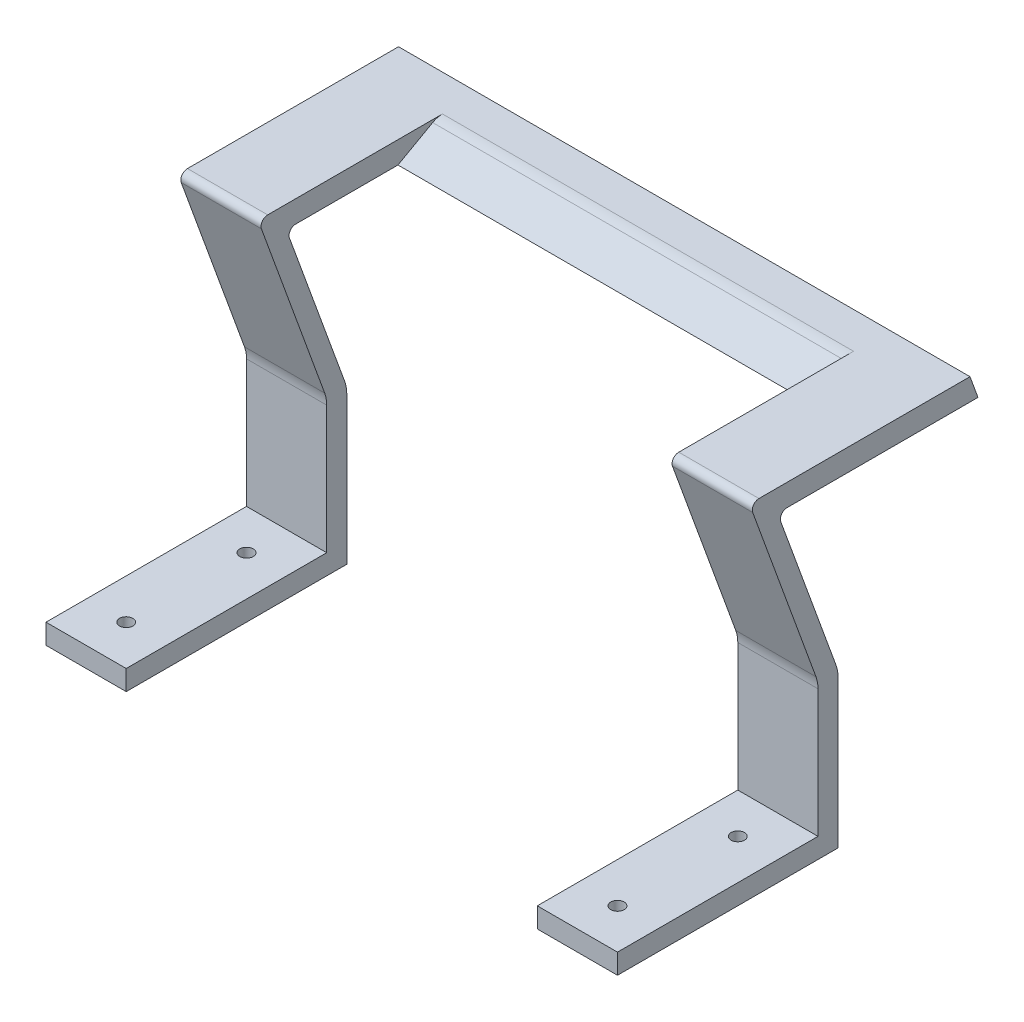
SolidWorks part; units mm, degrees
ref_plane "Front Plane" through (0, 0, 0) normal (0, 0, 1) x (1, 0, 0)
ref_plane "Top Plane" through (0, 0, 0) normal (0, 1, 0) x (1, 0, 0)
ref_plane "Right Plane" through (0, 0, 0) normal (1, 0, 0) x (0, 0, -1)
sketch "Sketch1" plane through (0, 0, 0) normal (0, 1, 0) x (1, 0, 0)
  line L0 (0, 0) -> (0, 33)
  line L1 (0, 33) -> (12, 33)
  line L2 (12, 33) -> (12, 0)
  line L3 (12, 0) -> (0, 0)
  line L4 (73.5, 33) -> (73.5, 0)
  line L5 (73.5, 0) -> (85.5, 0)
  line L6 (85.5, 0) -> (85.5, 33)
  line L7 (85.5, 33) -> (73.5, 33)
  circle A0 centre (6, 24) radius 1
  circle A1 centre (6, 6) radius 1
  circle A2 centre (79.5, 24) radius 1
  circle A3 centre (79.5, 6) radius 1
  point P17 (0, 0)
  point P18 (0, 0)
  point P19 (0, 0)
  point P20 (0, 0)
  point P21 (0, 0)
  dimension "D10" = 6
  dimension "D11" = 2
  dimension "D12" = 2
  dimension "D13" = 2
  dimension "D14" = 2
  dimension "D1" = 33
  dimension "D2" = 12
  dimension "D3" = 12
  dimension "D4" = 61.5
  dimension "D5" = 9
  dimension "D6" = 18
  dimension "D7" = 9
  dimension "D8" = 18
  dimension "D9" = 6
extrude "Boss-Extrude1" add sketch "Sketch1" along normal blind 3
sketch "Sketch2" plane through (0, 3, 0) normal (0, 1, 0) x (1, 0, 0)
  line L0 (0, 33) -> (0, 30)
  line L1 (0, 33) -> (0, 0) construction
  line L2 (0, 30) -> (12, 30)
  line L3 (12, 0) -> (12, 33) construction
  line L4 (12, 30) -> (12, 33)
  line L5 (12, 33) -> (0, 33)
  line L6 (73.5, 33) -> (85.5, 33)
  line L7 (85.5, 33) -> (85.5, 30)
  line L8 (85.5, 0) -> (85.5, 33) construction
  line L9 (85.5, 30) -> (73.5, 30)
  line L10 (73.5, 33) -> (73.5, 0) construction
  line L11 (73.5, 30) -> (73.5, 33)
  dimension "D1" = 3
extrude "Boss-Extrude2" add sketch "Sketch2" along normal blind 20
sketch "Sketch3" plane through (0, 23, 0) normal (0, 1, 0) x (1, 0, 0)
  line L0 (73.5, 33) -> (73.5, 30)
  line L1 (73.5, 30) -> (85.5, 30)
  line L2 (85.5, 30) -> (85.5, 33)
  line L3 (85.5, 33) -> (73.5, 33)
  line L4 (0, 33) -> (12, 33)
  line L5 (12, 33) -> (12, 30)
  line L6 (12, 30) -> (0, 30)
  line L7 (0, 30) -> (0, 33)
sketch "Sketch4" plane through (0, 0, 0) normal (1, 0, 0) x (0, 0, -1)
  line L0 (30, 23) -> (22.5453, 43.4817) construction
  line L1 (30, 23) -> (33, 23) construction
  dimension "D1" = 110
extrude "Boss-Extrude3" add sketch "Sketch3" along direction (0, 0.9397, 0.342) on the side of the normal blind 30
sketch "Sketch5" plane through (0, 13.2965, -36.5318) normal (0, 0.342, -0.9397) x (-1, 0, 0)
  line L0 (-85.5, 40.3263) -> (-85.5, 36.8263)
  line L1 (-85.5, 40.3263) -> (-85.5, 10.3263) construction
  line L2 (-85.5, 36.8263) -> (-73.5, 36.8263)
  line L3 (-73.5, 40.3263) -> (-73.5, 10.3263) construction
  line L4 (-73.5, 36.8263) -> (-73.5, 40.3263)
  line L5 (-73.5, 40.3263) -> (-85.5, 40.3263)
  line L6 (-12, 40.3263) -> (0, 40.3263)
  line L7 (0, 40.3263) -> (0, 36.8263)
  line L8 (0, 40.3263) -> (0, 10.3263) construction
  line L9 (0, 36.8263) -> (-12, 36.8263)
  line L10 (-12, 40.3263) -> (-12, 10.3263) construction
  line L11 (-12, 36.8263) -> (-12, 40.3263)
  dimension "D1" = 3.5
extrude "Boss-Extrude4" add sketch "Sketch5" along direction (0, 0, -1) on the side of the normal blind 30
sketch "Sketch6" plane through (12, 0, 0) normal (1, 0, 0) x (0, 0, -1)
  line L0 (53.9365, 47.9019) -> (52.7394, 51.1908)
  line L1 (52.7394, 51.1908) -> (46.5339, 51.1908)
  line L2 (19.7394, 51.1908) -> (52.7394, 51.1908) construction
  line L6 (53.9365, 47.9019) -> (40.6602, 47.9019)
  line L7 (53.9365, 47.9019) -> (23.9365, 47.9019) construction
  line L9 (53.9365, 47.9019) -> (23.9365, 47.9019) construction
  line L10 (19.7394, 51.1908) -> (52.7394, 51.1908) construction
  line L11 (46.5339, 51.1908) -> (40.6602, 47.9019)
  point P4 (38.9409, 51.1908)
  point P13 (32.909, 47.9019)
  point P16 (38.0243, 51.1908)
  point P17 (32.1506, 47.9019)
extrude "Boss-Extrude5" add sketch "Sketch6" along normal blind 61.5
fillet "Fillet2" radius 1 2 edges at (79.5, 51.1908, -19.7394) (6, 51.1908, -19.7394)
fillet "Fillet3" radius 3 1 edges at (42.75, 51.1908, -46.5339)
fillet "Fillet4" radius 5 2 edges at (6, 23, -33) (79.5, 23, -33)
fillet "Fillet5" radius 5 2 edges at (6, 23, -30) (79.5, 23, -30)
fillet "Fillet6" radius 1 2 edges at (6, 47.9019, -23.9365) (79.5, 47.9019, -23.9365)
